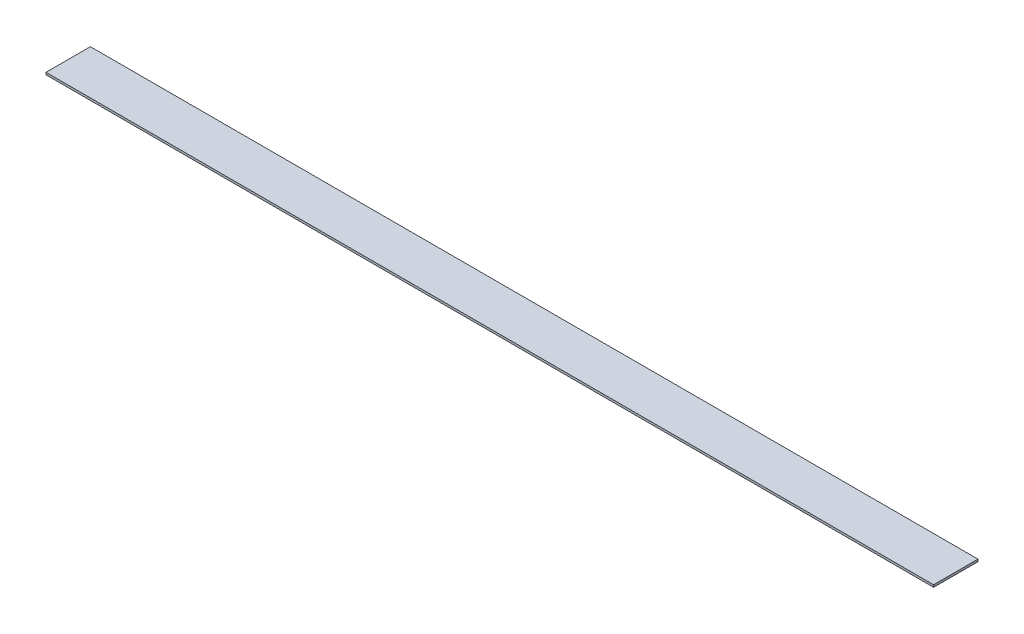
SolidWorks part; units mm, degrees
ref_plane "Alzado" through (0, 0, 0) normal (0, 0, 1) x (1, 0, 0)
ref_plane "Planta" through (0, 0, 0) normal (0, 1, 0) x (1, 0, 0)
ref_plane "Vista lateral" through (0, 0, 0) normal (1, 0, 0) x (0, 0, -1)
sketch "Croquis1" plane through (0, 0, 0) normal (0, 1, 0) x (1, 0, 0)
  line L1 (-20000, 1000) -> (20000, 1000)
  line L2 (-20000, 1000) -> (-20000, -1000)
  line L3 (-20000, -1000) -> (20000, -1000)
  line L4 (20000, 1000) -> (20000, -1000)
  line L5 (-20000, 1000) -> (20000, -1000) construction
  line L6 (-20000, -1000) -> (20000, 1000) construction
  point P0 (0, 0)
  dimension "D1" = 40000
  dimension "D2" = 2000
extrude "Saliente-Extruir1" add sketch "Croquis1" along normal blind 100
sketch "Croquis2" plane through (0, 100, 0) normal (0, 1, 0) x (1, 0, 0)
  line L0 (20000, 1000) -> (-20000, 1000) construction
  line L1 (-19123.9382, 1000) -> (-19023.9382, 1000)
  line L2 (-19123.9382, 1000) -> (-19123.9382, -1000)
  line L3 (-19123.9382, -1000) -> (-19023.9382, -1000)
  line L4 (-19023.9382, 1000) -> (-19023.9382, -1000)
  line L5 (-20000, -1000) -> (20000, -1000) construction
  line L14 (-13200.6123, -266.8851) -> (-12417.2305, 116.8122)
  line L15 (-13200.6123, -266.8851) -> (-13257.0005, -151.7593)
  line L16 (-12417.2305, 116.8122) -> (-12473.6186, 231.938)
  line L17 (-13257.0005, -151.7593) -> (-12473.6186, 231.938)
  line L23 (-8049.6553, -1000) -> (-7868.7781, -1000)
  line L24 (-8049.6553, -1000) -> (-8049.6553, 1000)
  line L25 (-8049.6553, 1000) -> (-7868.7781, 1000)
  line L26 (-7868.7781, -1000) -> (-7868.7781, 1000)
  line L30 (-4111.6032, 231.938) -> (-3644.07, -266.8851)
  line L31 (-4111.6032, 231.938) -> (-3892.0622, 437.7078)
  line L32 (-3644.07, -266.8851) -> (-3424.529, -61.1153)
  line L33 (-3892.0622, 437.7078) -> (-3424.529, -61.1153)
  line L39 (3655.3213, 1000) -> (3799.2174, 1000)
  line L40 (3655.3213, 1000) -> (3655.3213, -1000)
  line L41 (3655.3213, -1000) -> (3799.2174, -1000)
  line L42 (3799.2174, 1000) -> (3799.2174, -1000)
  line L47 (10167.1093, 1000) -> (10386.746, 1000)
  line L48 (10167.1093, 1000) -> (10167.1093, -1000)
  line L49 (10167.1093, -1000) -> (10386.746, -1000)
  line L50 (10386.746, 1000) -> (10386.746, -1000)
  line L54 (-17438.4091, 437.7078) -> (-17093.0981, -388.5005)
  line L55 (-17438.4091, 437.7078) -> (-17389.308, 458.2294)
  line L56 (-17093.0981, -388.5005) -> (-17043.997, -367.9789)
  line L57 (-17389.308, 458.2294) -> (-17043.997, -367.9789)
  line L58 (-15509.7818, -367.9789) -> (-15663.9914, -266.8851)
  line L59 (-15509.7818, -367.9789) -> (-15061.6538, 315.6007)
  line L60 (-15663.9914, -266.8851) -> (-15215.8634, 416.6945)
  line L61 (-15061.6538, 315.6007) -> (-15215.8634, 416.6945)
  line L62 (-10543.6032, 416.6945) -> (-10693.3822, 366.1476)
  line L63 (-10543.6032, 416.6945) -> (-10289.5004, -336.2551)
  line L64 (-10693.3822, 366.1476) -> (-10439.2795, -386.802)
  line L65 (-10289.5004, -336.2551) -> (-10439.2795, -386.802)
  line L66 (-5806.7253, 391.421) -> (-5586.2729, 315.6007)
  line L67 (-5806.7253, 391.421) -> (-6047.5764, -308.8684)
  line L68 (-5586.2729, 315.6007) -> (-5827.124, -384.6888)
  line L69 (-6047.5764, -308.8684) -> (-5827.124, -384.6888)
  line L70 (-1403.439, 437.7078) -> (-1403.439, -384.6888)
  line L71 (-1403.439, 437.7078) -> (-1289.1565, 437.7078)
  line L72 (-1403.439, -384.6888) -> (-1289.1565, -384.6888)
  line L73 (-1289.1565, 437.7078) -> (-1289.1565, -384.6888)
  line L74 (1682.8723, 315.6007) -> (1785.3191, 391.421)
  line L75 (1682.8723, 315.6007) -> (2232.2776, -426.7441)
  line L76 (1785.3191, 391.421) -> (2334.7244, -350.9237)
  line L77 (2232.2776, -426.7441) -> (2334.7244, -350.9237)
  line L78 (5296.7959, 492.3073) -> (5192.5023, 457.1107)
  line L79 (5296.7959, 492.3073) -> (5580.6175, -348.7042)
  line L80 (5192.5023, 457.1107) -> (5476.3239, -383.9009)
  line L81 (5580.6175, -348.7042) -> (5476.3239, -383.9009)
  line L82 (8191.4342, -426.7441) -> (8065.785, -383.9009)
  line L83 (8191.4342, -426.7441) -> (8465.8363, 378.0133)
  line L84 (8065.785, -383.9009) -> (8340.1871, 420.8565)
  line L85 (8465.8363, 378.0133) -> (8340.1871, 420.8565)
  line L86 (12135.0834, 378.0133) -> (12448.464, -426.7441)
  line L87 (12135.0834, 378.0133) -> (12222.2869, 411.9712)
  line L88 (12448.464, -426.7441) -> (12535.6674, -392.7862)
  line L89 (12222.2869, 411.9712) -> (12535.6674, -392.7862)
  line L90 (13771.057, 411.9712) -> (14066.5006, -346.7242)
  line L91 (13771.057, 411.9712) -> (13652.6133, 365.848)
  line L92 (14066.5006, -346.7242) -> (13948.0569, -392.8474)
  line L93 (13652.6133, 365.848) -> (13948.0569, -392.8474)
  line L94 (15767.3425, 315.6007) -> (16382.6253, -266.8851)
  line L95 (15767.3425, 315.6007) -> (15822.3611, 373.7172)
  line L96 (16382.6253, -266.8851) -> (16437.6439, -208.7686)
  line L97 (15822.3611, 373.7172) -> (16437.6439, -208.7686)
  line L98 (17597.9615, 373.7172) -> (17672.1274, -346.7242)
  line L99 (17597.9615, 373.7172) -> (17736.9134, 388.0216)
  line L100 (17672.1274, -346.7242) -> (17811.0792, -332.4198)
  line L101 (17736.9134, 388.0216) -> (17811.0792, -332.4198)
  dimension "D1" = 100
sketch "Croquis3" plane through (0, 100, 0) normal (0, 1, 0) x (1, 0, 0)
  circle A0 centre (-16527.7466, 627.6907) radius 152.1084
  circle A1 centre (-14473.6235, -112.749) radius 170.3882
  circle A2 centre (-11694.9842, 556.0353) radius 149.5871
  circle A3 centre (-9187.0432, -283.1372) radius 124.0966
  circle A4 centre (-16527.7466, -453.459) radius 107.7681
  circle A5 centre (-12713.0492, -561.2271) radius 114.5555
  circle A6 centre (-13274.8549, 248.7981) radius 113.8953
  circle A7 centre (-15488.6368, 322.3678) radius 109.694
  circle A8 centre (-11435.6101, -283.1372) radius 130.3581
sketch "Croquis4" plane through (0, 100, 0) normal (0, 1, 0) x (1, 0, 0)
  line L0 (-2782.8397, -722.0882) -> (-1999.4067, 596.3722)
  line L1 (-7196.8158, 711.0209) -> (-7053.5049, 711.0209)
  line L2 (-7196.8158, 711.0209) -> (-7196.8158, -808.0748)
  line L3 (-7196.8158, -808.0748) -> (-7053.5049, -808.0748)
  line L4 (-7053.5049, 711.0209) -> (-7053.5049, -808.0748)
  line L5 (-2782.8397, -722.0882) -> (-2918.1242, -641.7018)
  line L6 (-1999.4067, 596.3722) -> (-2134.6912, 676.7586)
  line L7 (-2918.1242, -641.7018) -> (-2134.6912, 676.7586)
  line L8 (-270.1217, 768.3453) -> (694.8384, -722.0882)
  line L9 (-270.1217, 768.3453) -> (-76.0551, 893.991)
  line L10 (694.8384, -722.0882) -> (888.905, -596.4425)
  line L11 (-76.0551, 893.991) -> (888.905, -596.4425)
